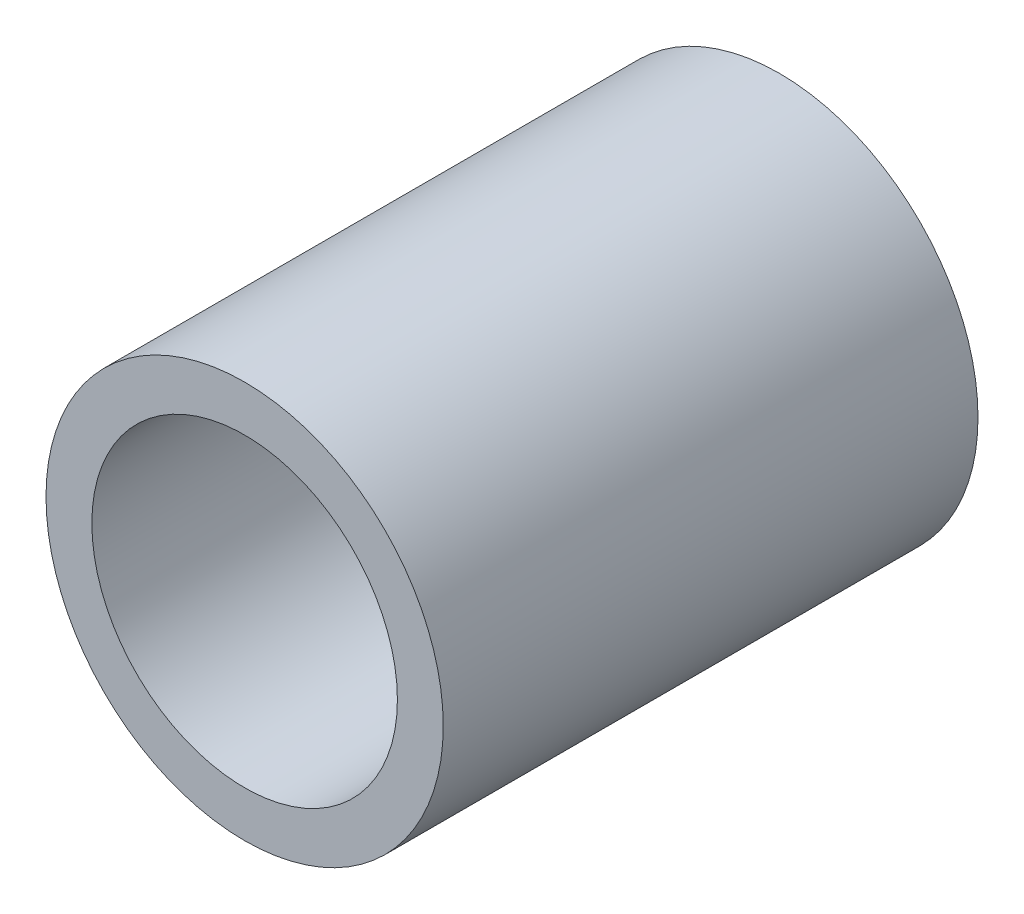
SolidWorks part; units mm, degrees
ref_plane "Front Plane" through (0, 0, 0) normal (0, 0, 1) x (1, 0, 0)
ref_plane "Top Plane" through (0, 0, 0) normal (0, 1, 0) x (1, 0, 0)
ref_plane "Right Plane" through (0, 0, 0) normal (1, 0, 0) x (0, 0, -1)
sketch "Sketch1" plane through (0, 0, 0) normal (0, 0, 1) x (1, 0, 0)
  circle A1 centre (0, 0) radius 10
  circle A2 centre (0, 0) radius 13
extrude "Boss-Extrude1" add sketch "Sketch1" along normal blind 35
